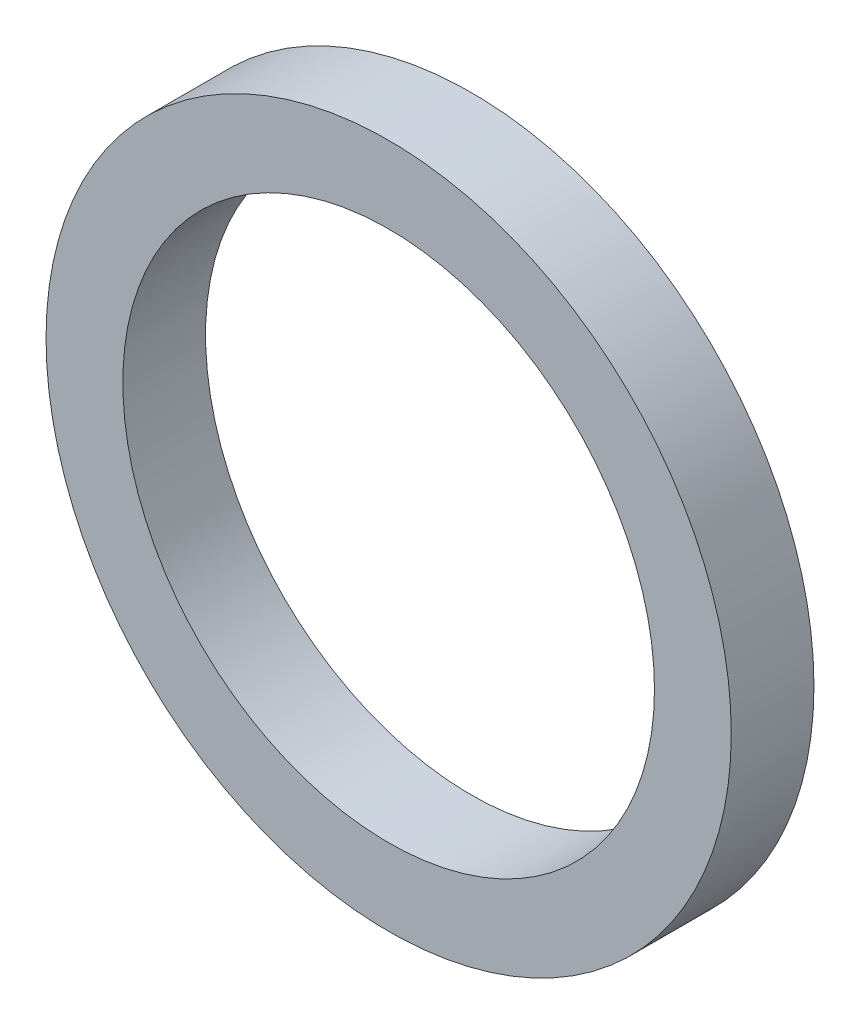
SolidWorks part; units mm, degrees
material "Alloy Steel (SS)"
ref_plane "Front Plane" through (0, 0, 0) normal (0, 0, 1) x (1, 0, 0)
ref_plane "Top Plane" through (0, 0, 0) normal (0, 1, 0) x (1, 0, 0)
ref_plane "Right Plane" through (0, 0, 0) normal (1, 0, 0) x (0, 0, -1)
sketch "Sketch1" plane through (0, 0, 0) normal (0, 0, 1) x (1, 0, 0)
  circle A0 centre (0, 0) radius 22.5
  circle A1 centre (0, 0) radius 29
  dimension "D1" = 58
  dimension "D2" = 45
extrude "Boss-Extrude1" add sketch "Sketch1" along normal blind 7
